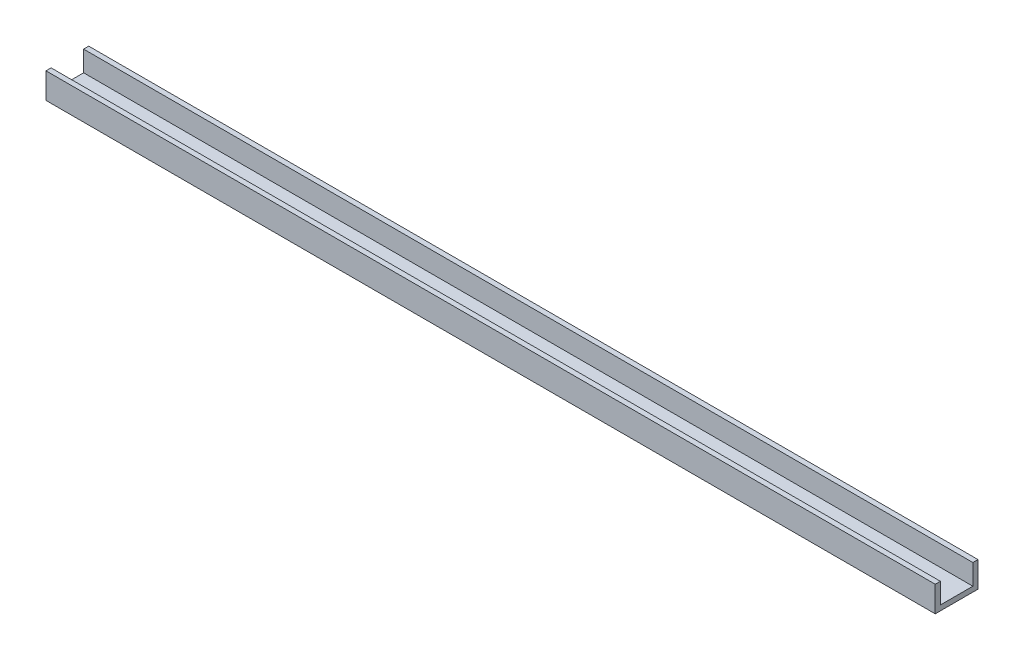
SolidWorks part; units mm, degrees
ref_plane "Спереди" through (0, 0, 0) normal (0, 0, 1) x (1, 0, 0)
ref_plane "Сверху" through (0, 0, 0) normal (0, 1, 0) x (1, 0, 0)
ref_plane "Справа" through (0, 0, 0) normal (1, 0, 0) x (0, 0, -1)
sketch "Эскиз1" plane through (0, 0, 0) normal (1, 0, 0) x (0, 0, -1)
  line L0 (-12.5, 0) -> (12.5, 0)
  line L1 (12.5, 0) -> (12.5, 15)
  line L2 (0, 29.661) -> (0, -35.101) construction
  line L3 (-12.5, 0) -> (-12.5, 15)
  point P8 (0, 0)
extrude "Вытянуть-Тонкостенный1" add sketch "Эскиз1" along normal blind 520 thin thin type one direction wall 3
